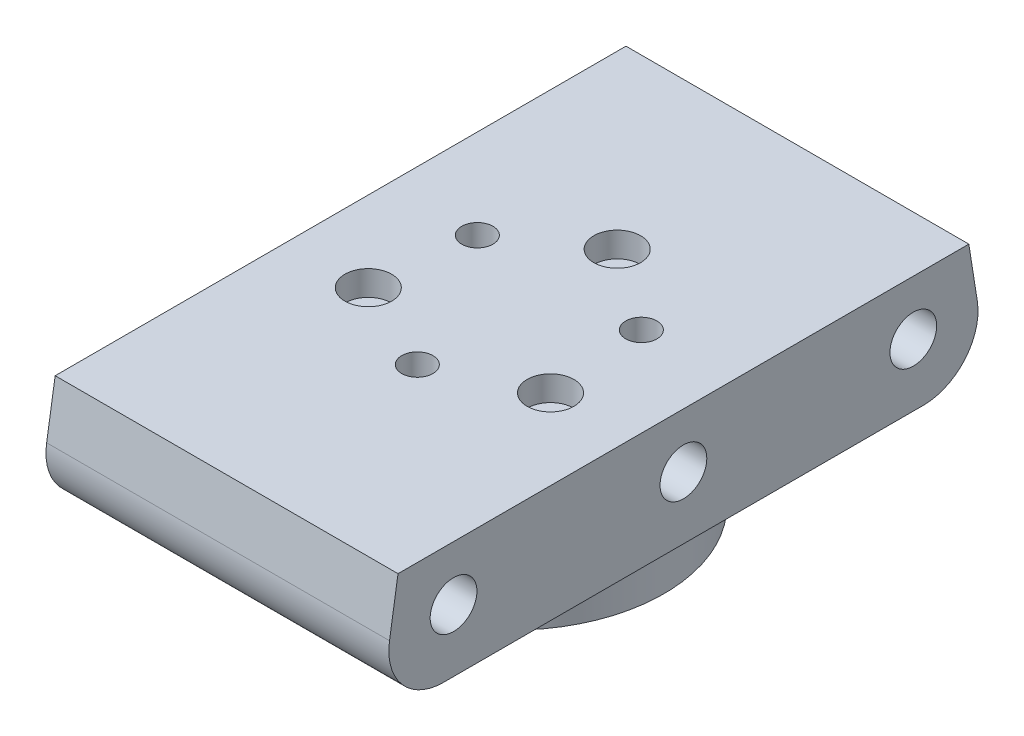
SolidWorks part; units mm, degrees
material "6061 合金"
ref_plane "前视基准面" through (0, 0, 0) normal (0, 0, 1) x (1, 0, 0)
ref_plane "上视基准面" through (0, 0, 0) normal (0, 1, 0) x (1, 0, 0)
ref_plane "右视基准面" through (0, 0, 0) normal (1, 0, 0) x (0, 0, -1)
sketch "草图1" plane through (0, 0, 0) normal (0, 1, 0) x (1, 0, 0)
  line L1 (0, -12.15) -> (10.5222, 6.075) construction
  line L2 (10.5222, 6.075) -> (-10.5222, 6.075) construction
  line L3 (-10.5222, 6.075) -> (0, -12.15) construction
  line L4 (-11.6913, -6.75) -> (11.6913, -6.75) construction
  line L5 (11.6913, -6.75) -> (0, 13.5) construction
  line L6 (0, 13.5) -> (-11.6913, -6.75) construction
  circle A0 centre (0, 0) radius 19.5
  circle A1 centre (0, 0) radius 13.5 construction
  circle A2 centre (0, 0) radius 12.15 construction
  circle A3 centre (0, 0) radius 6.075 construction
  circle A4 centre (0, 0) radius 6.75 construction
  circle A5 centre (10.5222, 6.075) radius 2
  circle A6 centre (-10.5222, 6.075) radius 2
  circle A7 centre (0, -12.15) radius 2
  circle A8 centre (0, 13.5) radius 1.5
  circle A9 centre (11.6913, -6.75) radius 1.5
  circle A10 centre (-11.6913, -6.75) radius 1.5
  dimension "D1" = 39
  dimension "D2" = 24.3
  dimension "D3" = 27
  dimension "D4" = 4
  dimension "D5" = 3
extrude "凸台-拉伸1" add sketch "草图1" along normal blind 6.8
sketch "草图2" plane through (0, 6.8, 0) normal (0, 1, 0) x (1, 0, 0)
  line L1 (-22, 39) -> (22, 39)
  line L2 (-22, 39) -> (-22, -39)
  line L3 (-22, -39) -> (22, -39)
  line L4 (22, 39) -> (22, -39)
  line L5 (-22, 39) -> (22, -39) construction
  line L6 (-22, -39) -> (22, 39) construction
  line L7 (-7.5, 39) -> (7.5, 39) construction
  line L8 (-7.5, 39) -> (-7.5, -39) construction
  line L9 (-7.5, -39) -> (7.5, -39) construction
  line L10 (7.5, 39) -> (7.5, -39) construction
  line L11 (-7.5, 39) -> (7.5, -39) construction
  line L12 (-7.5, -39) -> (7.5, 39) construction
  point P0 (0, 0)
  point P8 (0, 0)
  dimension "D1" = 15
  dimension "D2" = 22
  dimension "D3" = 78
extrude "凸台-拉伸2" add sketch "草图2" along normal blind 70
sketch "草图3" plane through (22, 0, 0) normal (1, 0, 0) x (0, 0, -1)
  line L0 (0, 47.8) -> (0, 0) construction
  line L1 (-25, 72.8) -> (25, 72.8) construction
  line L2 (-25, 72.8) -> (-25, 22.8) construction
  line L3 (-25, 22.8) -> (25, 22.8) construction
  line L4 (25, 72.8) -> (25, 22.8) construction
  line L5 (-25, 72.8) -> (25, 22.8) construction
  line L6 (-25, 22.8) -> (25, 72.8) construction
  line L8 (-22, 76.8) -> (22, 76.8) construction
  line L9 (-39, 76.8) -> (39, 76.8) construction
  line L10 (-39, 21.8) -> (39, 21.8) construction
  line L11 (-39, 76.8) -> (-39, 6.8) construction
  line L12 (39, 76.8) -> (39, 6.8) construction
  line L13 (-30.7981, 58.6432) -> (-39, 6.8) construction
  line L15 (-39, 6.8) -> (-36.6269, 21.8)
  line L16 (-36.6269, 21.8) -> (36.6269, 21.8)
  line L17 (0, 21.8) -> (0, 83.4986) construction
  line L18 (44.0818, 83.4986) -> (-44.0818, 83.4986)
  line L19 (-44.0818, 83.4986) -> (-44.0818, 6.8)
  line L20 (-44.0818, 6.8) -> (-39, 6.8)
  line L21 (44.0818, 83.4986) -> (44.0818, 6.8)
  line L22 (39, 6.8) -> (36.6269, 21.8)
  line L23 (44.0818, 6.8) -> (39, 6.8)
  arc A0 (-16, 72.8) -> (-25, 63.8) centre (-7.0929, 54.8929) ccw construction
  arc A1 (-17.7814, 76.3814) -> (-28.5814, 65.5814) centre (-7.0929, 54.8929) ccw construction
  arc A2 (-16.8949, 76.8) -> (-30.7981, 58.6432) centre (-7.0929, 54.8929) ccw construction
  circle A3 centre (0, 14.8) radius 3
  circle A4 centre (-29.5, 14.8) radius 3
  circle A5 centre (29.5, 14.8) radius 3
  point P0 (0, 47.8)
  point P17 (0, 76.8)
  dimension "D2" = 16
  dimension "D6" = 1
  dimension "D3" = 20
  dimension "D9" = 6
  dimension "D1" = 50
  dimension "D4" = 44
  dimension "D5" = 4
  dimension "D8" = 7
  dimension "D10" = 9.5
  dimension "D11" = 7
  dimension "D7" = 4
extrude "切除-拉伸1" cut sketch "草图3" against normal blind 12
sketch "草图5" plane through (10, 0, 0) normal (1, 0, 0) x (0, 0, -1)
  line L6 (-39, 6.8) -> (-36.6269, 21.8)
  line L7 (-36.6269, 21.8) -> (36.6269, 21.8)
  line L8 (36.6269, 21.8) -> (39, 6.8)
  line L9 (39, 6.8) -> (39, 76.8)
  line L10 (39, 76.8) -> (-39, 76.8)
  line L11 (-39, 76.8) -> (-39, 6.8)
  line L12 (-39, 6.8) -> (-36.6269, 21.8)
  line L13 (-36.6269, 21.8) -> (36.6269, 21.8)
  line L14 (36.6269, 21.8) -> (39, 6.8)
  line L15 (39, 6.8) -> (39, 76.8)
  line L16 (39, 76.8) -> (-39, 76.8)
  line L17 (-39, 76.8) -> (-39, 6.8)
  dimension "D1" = 0
extrude "切除-拉伸2" cut sketch "草图5" against normal through all
sketch "草图6" plane through (-22, 0, 0) normal (-1, 0, 0) x (0, 0, 1)
  circle A0 centre (-29.5, 14.8) radius 3 construction
  circle A1 centre (0, 14.8) radius 3 construction
  circle A2 centre (29.5, 14.8) radius 3 construction
  circle A3 centre (-29.5, 14.8) radius 3
  circle A4 centre (0, 14.8) radius 3
  circle A5 centre (29.5, 14.8) radius 3
extrude "切除-拉伸3" cut sketch "草图6" against normal blind 12
chamfer "倒角1" distance 2 angle 45 1 edges at (0, 6.8, 19.5)
fillet "圆角1" radius 7 2 edges at (0, 6.8, -39) (0, 6.8, 39)
sketch "草图7" plane through (0, 21.8, 0) normal (0, 1, 0) x (1, 0, 0)
  circle A0 centre (10.5222, 6.075) radius 2 construction
  circle A1 centre (11.6913, -6.75) radius 1.5 construction
  circle A2 centre (0, -12.15) radius 2 construction
  circle A3 centre (-11.6913, -6.75) radius 1.5 construction
  circle A4 centre (-10.5222, 6.075) radius 2 construction
  circle A5 centre (0, 13.5) radius 1.5 construction
  circle A6 centre (10.5222, 6.075) radius 2
  circle A7 centre (11.6913, -6.75) radius 1.5
  circle A8 centre (0, -12.15) radius 2
  circle A9 centre (-11.6913, -6.75) radius 1.5
  circle A10 centre (-10.5222, 6.075) radius 2
  circle A11 centre (0, 13.5) radius 1.5
extrude "切除-拉伸4" cut sketch "草图7" against normal through all
sketch "草图8" plane through (0, 21.8, 0) normal (0, 1, 0) x (1, 0, 0)
  circle A0 centre (0, 13.5) radius 3
  circle A1 centre (11.6913, -6.75) radius 3
  circle A2 centre (-11.6913, -6.75) radius 3
  dimension "D1" = 6
extrude "切除-拉伸5" cut sketch "草图8" against normal blind 3.2
